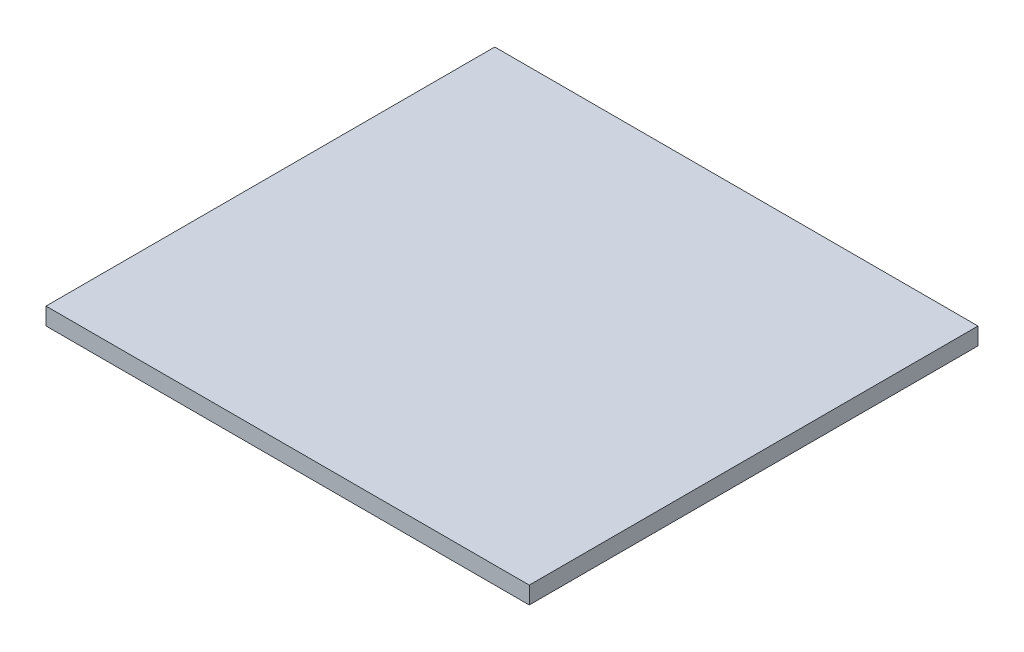
SolidWorks part; units mm, degrees
ref_plane "Front Plane" through (0, 0, 0) normal (0, 0, 1) x (1, 0, 0)
ref_plane "Top Plane" through (0, 0, 0) normal (0, 1, 0) x (1, 0, 0)
ref_plane "Right Plane" through (0, 0, 0) normal (1, 0, 0) x (0, 0, -1)
sketch "Sketch1" plane through (0, 0, 0) normal (0, 1, 0) x (1, 0, 0)
  line L1 (-77.3043, 43.6739) -> (62.6957, 43.6739)
  line L2 (-77.3043, 43.6739) -> (-77.3043, -86.3261)
  line L3 (-77.3043, -86.3261) -> (62.6957, -86.3261)
  line L4 (62.6957, 43.6739) -> (62.6957, -86.3261)
  line L5 (-7.3043, -86.3261) -> (-7.3043, 43.6739) construction
  line L6 (-77.3043, -21.3261) -> (62.6957, -21.3261) construction
  point P0 (-7.3043, -21.3261)
  dimension "D1" = 140
  dimension "D2" = 130
extrude "Boss-Extrude1" add sketch "Sketch1" along normal blind 5
